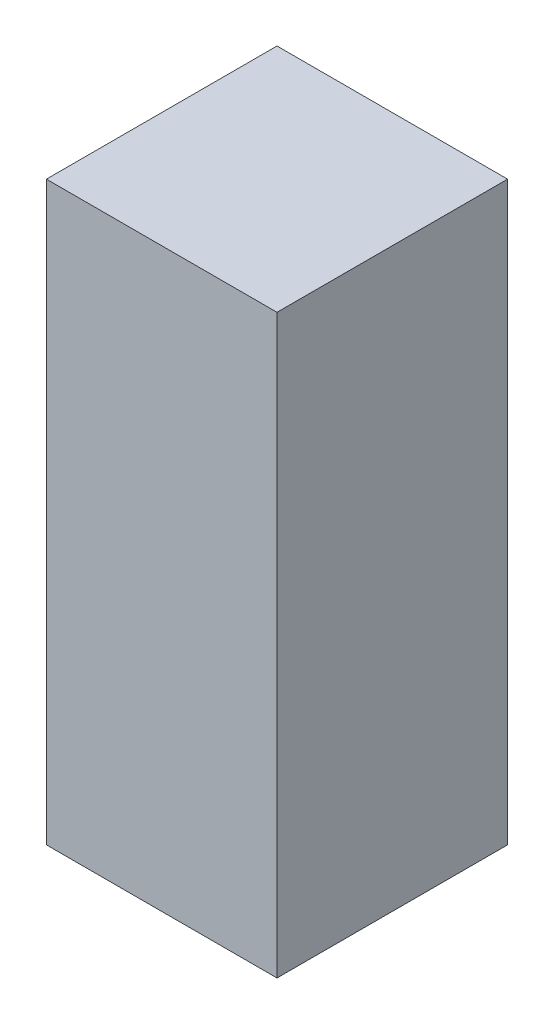
SolidWorks part; units mm, degrees
ref_plane "Front Plane" through (0, 0, 0) normal (0, 0, 1) x (1, 0, 0)
ref_plane "Top Plane" through (0, 0, 0) normal (0, 1, 0) x (1, 0, 0)
ref_plane "Right Plane" through (0, 0, 0) normal (1, 0, 0) x (0, 0, -1)
sketch "Sketch1" plane through (0, 0, 0) normal (0, 1, 0) x (1, 0, 0)
  line L1 (0, 4) -> (4, 4)
  line L2 (0, 4) -> (0, 0)
  line L3 (0, 0) -> (4, 0)
  line L4 (4, 4) -> (4, 0)
  dimension "D1" = 4
  dimension "D2" = 4
extrude "Boss-Extrude1" add sketch "Sketch1" along normal blind 10
